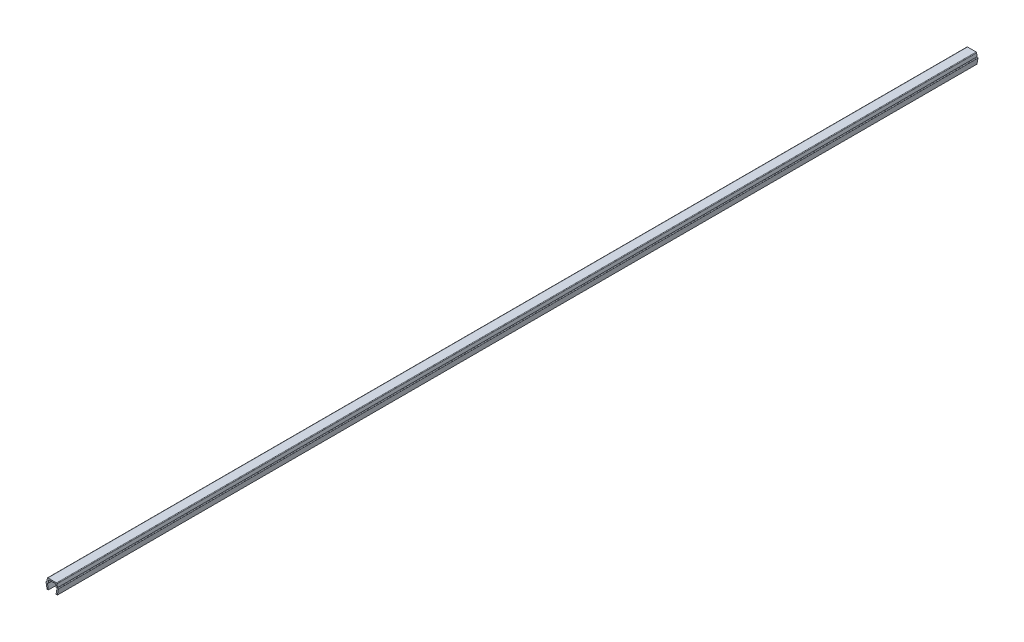
SolidWorks part; units mm, degrees
ref_plane "Front Plane" through (0, 0, 0) normal (0, 0, 1) x (1, 0, 0)
ref_plane "Top Plane" through (0, 0, 0) normal (0, 1, 0) x (1, 0, 0)
ref_plane "Right Plane" through (0, 0, 0) normal (1, 0, 0) x (0, 0, -1)
ref_plane "Plane1" through (0, 0, 0) normal (0, 0, 1) x (1, 0, 0)
sketch "Sketch1" plane through (0, 0, 0) normal (0, 0, 1) x (1, 0, 0)
  line L0 (-3.6, 3.35) -> (-3, 0)
  line L1 (-3, 0) -> (-2.2, 0)
  line L2 (-2.2, 0) -> (-2.7352, 2.9883)
  line L3 (-2.3907, 3.4) -> (-2.2, 3.4)
  line L4 (-2.2, 3.4) -> (-2.0705, 4.8805)
  line L5 (-1.7218, 5.2) -> (1.7218, 5.2)
  line L6 (2.0705, 4.8805) -> (2.2, 3.4)
  line L7 (2.2, 3.4) -> (2.3907, 3.4)
  line L8 (2.7352, 2.9883) -> (2.2, 0)
  line L9 (2.2, 0) -> (3, 0)
  line L10 (3, 0) -> (3.6, 3.35)
  line L11 (3.25, 3.7) -> (3, 3.7)
  line L12 (3, 3.7) -> (2.8355, 5.5805)
  line L13 (2.4868, 5.9) -> (-2.4868, 5.9)
  line L14 (-2.8355, 5.5805) -> (-3, 3.7)
  line L15 (-3, 3.7) -> (-3.25, 3.7)
  arc A0 (-2.7352, 2.9883) -> (-2.3907, 3.4) centre (-2.3907, 3.05) cw
  arc A1 (-2.0705, 4.8805) -> (-1.7218, 5.2) centre (-1.7218, 4.85) cw
  arc A2 (1.7218, 5.2) -> (2.0705, 4.8805) centre (1.7218, 4.85) cw
  arc A3 (2.3907, 3.4) -> (2.7352, 2.9883) centre (2.3907, 3.05) cw
  arc A4 (3.6, 3.35) -> (3.25, 3.7) centre (3.25, 3.35) ccw
  arc A5 (2.8355, 5.5805) -> (2.4868, 5.9) centre (2.4868, 5.55) ccw
  arc A6 (-2.4868, 5.9) -> (-2.8355, 5.5805) centre (-2.4868, 5.55) ccw
  arc A7 (-3.25, 3.7) -> (-3.6, 3.35) centre (-3.25, 3.35) ccw
extrude "Boss-Extrude1" add sketch "Sketch1" against normal mid plane 533.5
